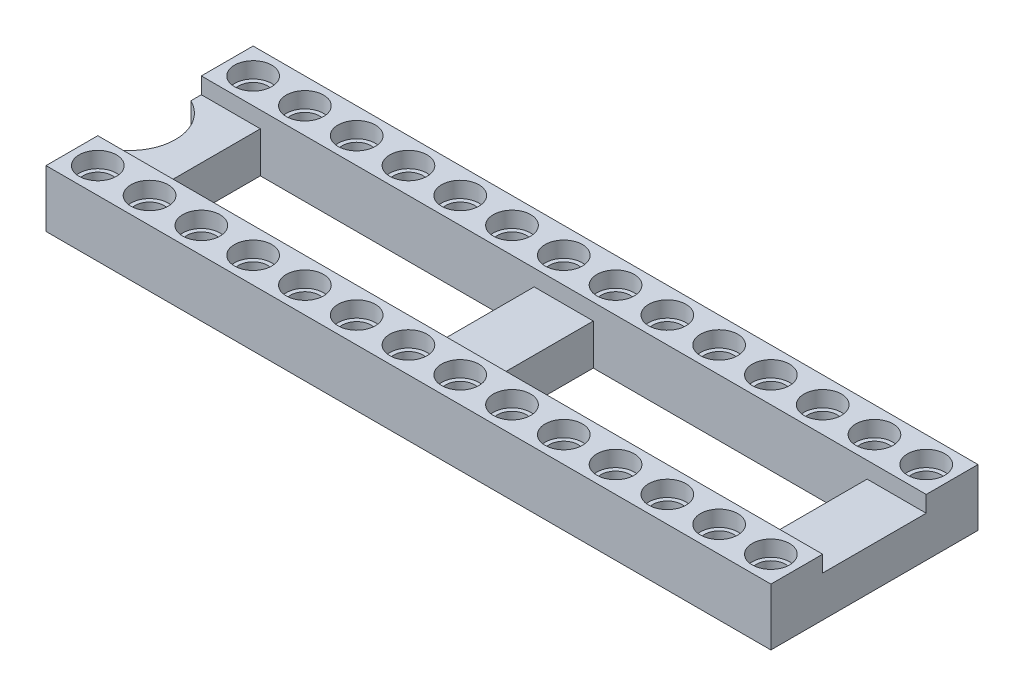
SolidWorks part; units mm, degrees
ref_plane "Front Plane" through (0, 0, 0) normal (0, 0, 1) x (1, 0, 0)
ref_plane "Top Plane" through (0, 0, 0) normal (0, 1, 0) x (1, 0, 0)
ref_plane "Right Plane" through (0, 0, 0) normal (1, 0, 0) x (0, 0, -1)
sketch "Sketch1" plane through (0, 0, 0) normal (0, 1, 0) x (1, 0, 0)
  line L1 (0, 0) -> (35.56, 0)
  line L2 (0, 0) -> (0, 10.16)
  line L3 (0, 10.16) -> (35.56, 10.16)
  line L4 (35.56, 0) -> (35.56, 10.16)
  dimension "D1" = 10.16
  dimension "D2" = 35.56
extrude "Boss-Extrude1" add sketch "Sketch1" along normal blind 2.8
sketch "Sketch3" plane through (0, 2.8, 0) normal (0, 1, 0) x (1, 0, 0)
  line L0 (35.56, 10.16) -> (0, 10.16) construction
  line L1 (0, 10.16) -> (0, 0) construction
  circle A0 centre (1.27, 8.89) radius 0.915
  circle A1 centre (3.81, 8.89) radius 0.915
  circle A2 centre (6.35, 8.89) radius 0.915
  circle A3 centre (8.89, 8.89) radius 0.915
  circle A4 centre (11.43, 8.89) radius 0.915
  circle A5 centre (13.97, 8.89) radius 0.915
  circle A6 centre (16.51, 8.89) radius 0.915
  circle A7 centre (19.05, 8.89) radius 0.915
  circle A8 centre (21.59, 8.89) radius 0.915
  circle A9 centre (24.13, 8.89) radius 0.915
  circle A10 centre (26.67, 8.89) radius 0.915
  circle A11 centre (29.21, 8.89) radius 0.915
  circle A12 centre (31.75, 8.89) radius 0.915
  circle A13 centre (34.29, 8.89) radius 0.915
  circle A14 centre (3.81, 1.27) radius 0.915
  circle A15 centre (6.35, 1.27) radius 0.915
  circle A16 centre (8.89, 1.27) radius 0.915
  circle A17 centre (11.43, 1.27) radius 0.915
  circle A18 centre (13.97, 1.27) radius 0.915
  circle A19 centre (16.51, 1.27) radius 0.915
  circle A20 centre (19.05, 1.27) radius 0.915
  circle A21 centre (21.59, 1.27) radius 0.915
  circle A22 centre (24.13, 1.27) radius 0.915
  circle A23 centre (26.67, 1.27) radius 0.915
  circle A24 centre (29.21, 1.27) radius 0.915
  circle A25 centre (31.75, 1.27) radius 0.915
  circle A26 centre (34.29, 1.27) radius 0.915
  circle A27 centre (1.27, 1.27) radius 0.915
  dimension "D1" = 1.83
  dimension "D4" = 1.27
  dimension "D5" = 1.27
  dimension "D2" = 14
  dimension "D3" = 2
extrude "Cut-Extrude1" cut sketch "Sketch3" against normal blind 0.78
sketch "Sketch4" plane through (0, 2.8, 0) normal (0, 1, 0) x (1, 0, 0)
  line L0 (0, 10.16) -> (0, 0) construction
  line L1 (0, 7.62) -> (35.56, 7.62)
  line L2 (0, 7.62) -> (0, 2.54)
  line L3 (0, 2.54) -> (35.56, 2.54)
  line L4 (35.56, 7.62) -> (35.56, 2.54)
  line L5 (35.56, 0) -> (35.56, 10.16) construction
  line L6 (0, 0) -> (35.56, 0) construction
  line L7 (35.56, 10.16) -> (0, 10.16) construction
  dimension "D2" = 2.54
  dimension "D1" = 2.54
extrude "Cut-Extrude2" cut sketch "Sketch4" against normal blind 0.8
sketch "Sketch5" plane through (0, 2, 0) normal (0, 1, 0) x (1, 0, 0)
  line L0 (1.27, 8.89) -> (1.27, 1.27) construction
  line L1 (1.27, 5.08) -> (-3.0448, 5.08) construction
  line L2 (35.56, 7.62) -> (0, 7.62) construction
  line L3 (2.895, 7.62) -> (16.3275, 7.62)
  line L4 (2.895, 7.62) -> (2.895, 2.54)
  line L5 (2.895, 2.54) -> (16.3275, 2.54)
  line L6 (16.3275, 7.62) -> (16.3275, 2.54)
  line L7 (0, 2.54) -> (35.56, 2.54) construction
  line L10 (35.56, 2.54) -> (35.56, 7.62) construction
  line L11 (19.2275, 7.62) -> (32.66, 7.62)
  line L12 (19.2275, 7.62) -> (19.2275, 2.54)
  line L13 (19.2275, 2.54) -> (32.66, 2.54)
  line L14 (32.66, 7.62) -> (32.66, 2.54)
  circle A0 centre (-0.98, 5.08) radius 2.25
  circle A1 centre (3.81, 8.89) radius 0.915 construction
  point P26 (35.56, 5.08)
  dimension "D1" = 4.5
  dimension "D2" = 0.915
  dimension "D3" = 2.9
  dimension "D4" = 2.9
extrude "Cut-Extrude3" cut sketch "Sketch5" against normal through all
sketch "Sketch6" plane through (0, 2.02, 0) normal (0, 1, 0) x (1, 0, 0)
  circle A0 centre (1.27, 8.89) radius 0.71
  circle A1 centre (3.81, 8.89) radius 0.71
  circle A2 centre (6.35, 8.89) radius 0.71
  circle A3 centre (8.89, 8.89) radius 0.71
  circle A4 centre (11.43, 8.89) radius 0.71
  circle A5 centre (13.97, 8.89) radius 0.71
  circle A6 centre (16.51, 8.89) radius 0.71
  circle A7 centre (19.05, 8.89) radius 0.71
  circle A8 centre (21.59, 8.89) radius 0.71
  circle A9 centre (24.13, 8.89) radius 0.71
  circle A10 centre (26.67, 8.89) radius 0.71
  circle A11 centre (29.21, 8.89) radius 0.71
  circle A12 centre (31.75, 8.89) radius 0.71
  circle A13 centre (34.29, 8.89) radius 0.71
  circle A14 centre (3.81, 1.27) radius 0.71
  circle A15 centre (6.35, 1.27) radius 0.71
  circle A16 centre (8.89, 1.27) radius 0.71
  circle A17 centre (11.43, 1.27) radius 0.71
  circle A18 centre (13.97, 1.27) radius 0.71
  circle A19 centre (16.51, 1.27) radius 0.71
  circle A20 centre (19.05, 1.27) radius 0.71
  circle A21 centre (21.59, 1.27) radius 0.71
  circle A22 centre (24.13, 1.27) radius 0.71
  circle A23 centre (26.67, 1.27) radius 0.71
  circle A24 centre (29.21, 1.27) radius 0.71
  circle A25 centre (31.75, 1.27) radius 0.71
  circle A26 centre (34.29, 1.27) radius 0.71
  circle A27 centre (1.27, 1.27) radius 0.71
  dimension "D1" = 1.42
  dimension "D2" = 14
  dimension "D3" = 2
extrude "Cut-Extrude4" cut sketch "Sketch6" against normal through all
